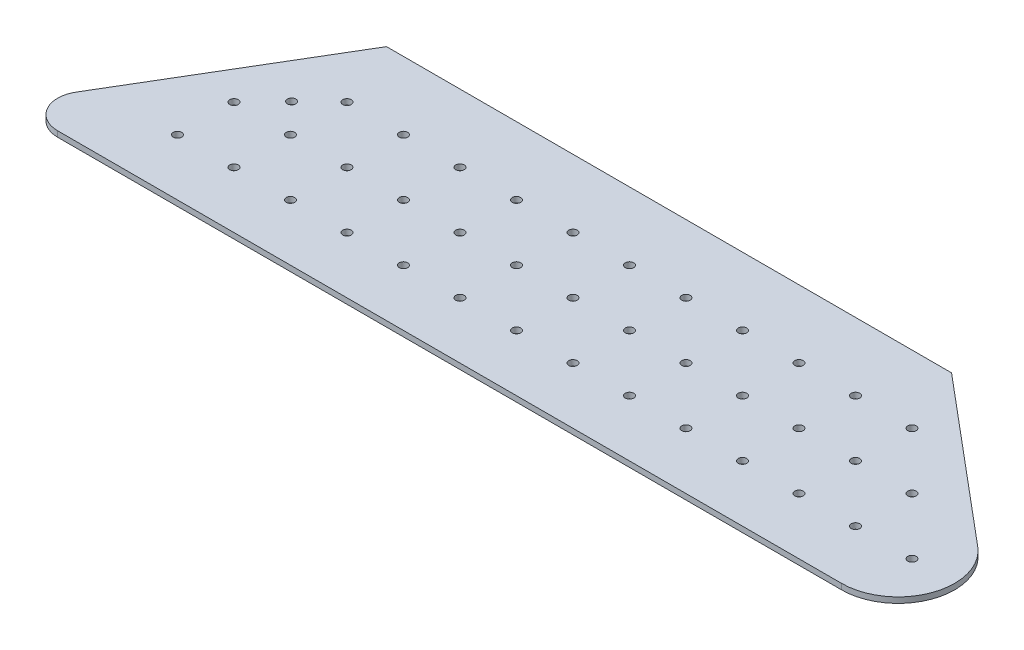
SolidWorks part; units mm, degrees
ref_plane "Front Plane" through (0, 0, 0) normal (0, 0, 1) x (1, 0, 0)
ref_plane "Top Plane" through (0, 0, 0) normal (0, 1, 0) x (1, 0, 0)
ref_plane "Right Plane" through (0, 0, 0) normal (1, 0, 0) x (0, 0, -1)
sketch "Sketch1" plane through (0, 0, 0) normal (0, 1, 0) x (1, 0, 0)
  line L0 (-17.984, 0) -> (332.016, 0)
  line L1 (-55, 0) -> (55, 0) construction
  line L2 (332.016, 0) -> (232.016, 84)
  line L3 (232.016, 84) -> (32.016, 84)
  line L4 (32.016, 84) -> (-17.984, 0)
  line L5 (-45.5557, 20) -> (286.5842, 20) construction
  line L6 (-34.9172, 40) -> (80.516, 40) construction
  line L7 (-27.9699, 60) -> (20.516, 60) construction
  line L8 (308.2064, 20) -> (439.4037, 20) construction
  line L9 (123.516, 40) -> (160.516, 40) construction
  line L10 (163.516, 40) -> (200.516, 40) construction
  line L11 (203.516, 40) -> (233.588, 40) construction
  line L12 (236.588, 40) -> (263.1596, 40) construction
  line L13 (266.1596, 40) -> (280.516, 40) construction
  line L14 (236.588, 60) -> (319.174, 60) construction
  line L15 (203.516, 60) -> (233.588, 60) construction
  line L16 (163.516, 60) -> (200.516, 60) construction
  line L17 (123.516, 60) -> (160.516, 60) construction
  line L18 (83.516, 60) -> (120.516, 60) construction
  line L19 (43.516, 60) -> (80.516, 60) construction
  line L20 (83.516, 40) -> (120.516, 40) construction
  line L21 (242.016, 20) -> (242.016, 12.284) construction
  line L22 (76.4385, 30) -> (108.1697, 30) construction
  line L23 (283.516, 40) -> (434.9926, 40) construction
  circle A0 centre (42.016, 20) radius 1.5
  circle A1 centre (62.016, 20) radius 1.5
  circle A2 centre (82.016, 20) radius 1.5
  circle A3 centre (102.016, 20) radius 1.5
  circle A4 centre (122.016, 20) radius 1.5
  circle A21 centre (22.016, 20) radius 1.5
  circle A22 centre (162.016, 20) radius 1.5
  circle A23 centre (182.016, 20) radius 1.5
  circle A24 centre (202.016, 20) radius 1.5
  circle A25 centre (222.016, 20) radius 1.5
  circle A26 centre (242.016, 20) radius 1.5
  circle A27 centre (142.016, 20) radius 1.5
  circle A28 centre (242.016, 60) radius 1.5
  circle A29 centre (222.016, 60) radius 1.5
  circle A30 centre (202.016, 60) radius 1.5
  circle A31 centre (182.016, 60) radius 1.5
  circle A32 centre (162.016, 60) radius 1.5
  circle A33 centre (142.016, 60) radius 1.5
  circle A34 centre (122.016, 60) radius 1.5
  circle A35 centre (102.016, 60) radius 1.5
  circle A36 centre (82.016, 60) radius 1.5
  circle A37 centre (62.016, 60) radius 1.5
  circle A38 centre (42.016, 60) radius 1.5
  circle A41 centre (282.016, 20) radius 1.5
  circle A42 centre (262.016, 20) radius 1.5
  circle A44 centre (262.016, 40) radius 1.5
  circle A45 centre (242.016, 40) radius 1.5
  circle A46 centre (202.016, 40) radius 1.5
  circle A47 centre (182.016, 40) radius 1.5
  circle A48 centre (162.016, 40) radius 1.5
  circle A49 centre (142.016, 40) radius 1.5
  circle A50 centre (122.016, 40) radius 1.5
  circle A51 centre (102.016, 40) radius 1.5
  circle A52 centre (82.016, 40) radius 1.5
  circle A53 centre (62.016, 40) radius 1.5
  circle A54 centre (42.016, 40) radius 1.5
  circle A55 centre (22.016, 40) radius 1.5
  circle A56 centre (222.016, 40) radius 1.5
  circle A57 centre (32.016, 50.3974) radius 1.5
  dimension "D13" = 3
  dimension "D14" = 3
  dimension "D15" = 3
  dimension "D16" = 3
  dimension "D17" = 3
  dimension "D18" = 20
  dimension "D19" = 10
  dimension "D20" = 40
  dimension "D21" = 60
  dimension "D22" = 80
  dimension "D23" = 100
  dimension "D24" = 20
  dimension "D25" = 0
  dimension "D26" = 32
  dimension "D27" = 3
  dimension "D28" = 3
  dimension "D29" = 10
  dimension "D34" = 20
  dimension "D1" = 350
  dimension "D2" = 84
  dimension "D3" = 100
  dimension "D4" = 200
  dimension "D5" = 20
  dimension "D6" = 40
  dimension "D7" = 60
  dimension "D8" = 60
  dimension "D9" = 80
  dimension "D10" = 100
  dimension "D11" = 120
  dimension "D12" = 140
extrude "Boss-Extrude1" add sketch "Sketch1" along normal blind 2
fillet "Fillet4" radius 20 1 edges at (332.016, 1, 0)
fillet "Fillet5" radius 10 1 edges at (-17.984, 1, 0)
